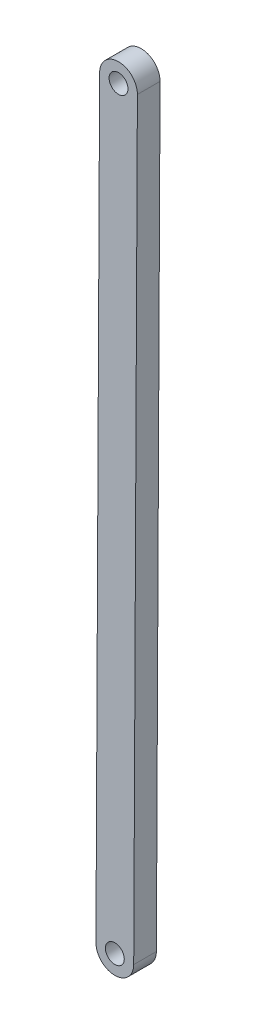
SolidWorks part; units mm, degrees
ref_plane "Front Plane" through (0, 0, 0) normal (0, 0, 1) x (1, 0, 0)
ref_plane "Top Plane" through (0, 0, 0) normal (0, 1, 0) x (1, 0, 0)
ref_plane "Right Plane" through (0, 0, 0) normal (1, 0, 0) x (0, 0, -1)
sketch "Sketch1" plane through (0, 0, 0) normal (0, 0, 1) x (1, 0, 0)
  line L0 (0, 0) -> (-1.9492, -400) construction
  line L1 (9.9999, -0.0487) -> (8.0507, -400.0487)
  line L2 (-9.9999, 0.0487) -> (-11.949, -399.9513)
  arc A0 (9.9999, -0.0487) -> (-9.9999, 0.0487) centre (0, 0) ccw
  arc A1 (-11.949, -399.9513) -> (8.0507, -400.0487) centre (-1.9492, -400) ccw
  circle A2 centre (-1.9492, -400) radius 5
  circle A3 centre (0, 0) radius 5
  point P3 (-0.9746, -200)
  dimension "D3" = 10
  dimension "D4" = 10
  dimension "D1" = 400
  dimension "D2" = 20
extrude "Boss-Extrude1" add sketch "Sketch1" along normal blind 6
mirror "Mirror1" about plane through (0, 0, 0) normal (0, 0, 1) of "Boss-Extrude1"
